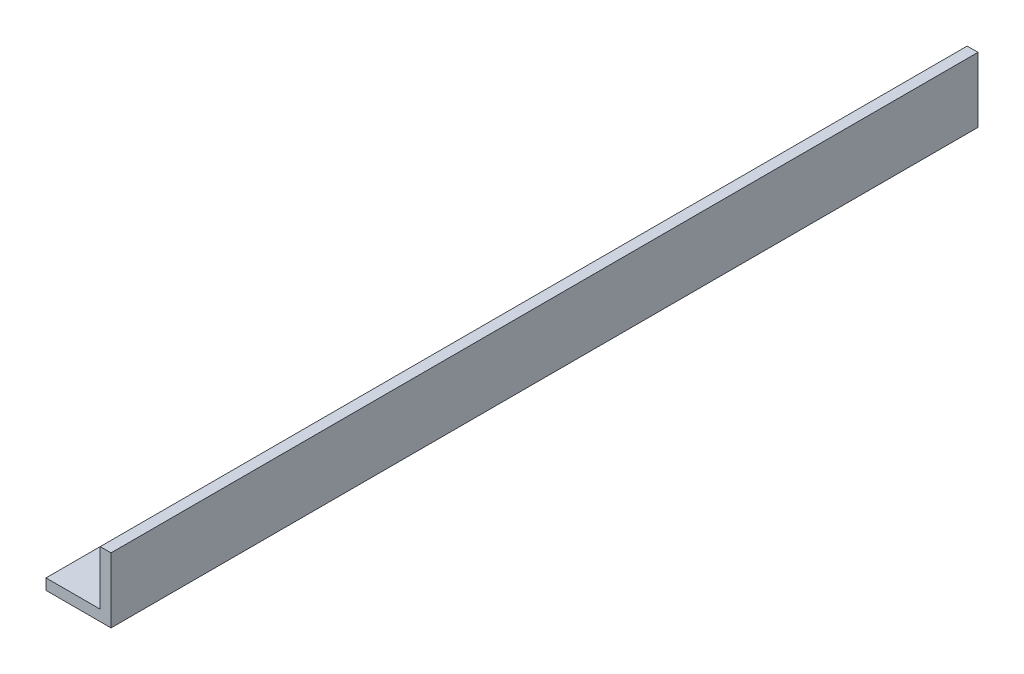
SolidWorks part; units mm, degrees
ref_plane "Front Plane" through (0, 0, 0) normal (0, 0, 1) x (1, 0, 0)
ref_plane "Top Plane" through (0, 0, 0) normal (0, 1, 0) x (1, 0, 0)
ref_plane "Right Plane" through (0, 0, 0) normal (1, 0, 0) x (0, 0, -1)
sketch "Sketch1" plane through (0, 0, 0) normal (0, 0, 1) x (1, 0, 0)
  line L0 (-4.7625, -4.7625) -> (4.7625, -4.7625) construction
  line L1 (4.7625, -4.7625) -> (4.7625, 4.7625) construction
  line L2 (4.7625, 4.7625) -> (3.175, 4.7625) construction
  line L3 (3.175, 4.7625) -> (3.175, -3.175) construction
  line L4 (3.175, -3.175) -> (-4.7625, -3.175) construction
  line L5 (-4.7625, -4.7625) -> (-4.7625, -3.175) construction
  line L6 (3.9688, 4.7625) -> (4.7625, 4.7625) construction
  line L7 (-4.7625, -3.9688) -> (-4.7625, -4.7625) construction
  line L8 (0, 0) -> (4.7625, 0) construction
  line L9 (0, 0) -> (0, -4.7625) construction
  point P3 (0, -4.7625)
  point P5 (3.175, -4.7625)
  point P8 (-4.7625, -4.7625)
  point P12 (-4.7625, -3.175)
  point P17 (3.175, 4.7625)
  dimension "Outside Height" = 9.525
  dimension "Outside Width" = 9.525
  dimension "Wall Thickness" = 1.5875
  dimension "Inside Width" = 7.9375
  dimension "Inside Height" = 7.9375
sketch "Sketch2" plane through (0, 0, 0) normal (1, 0, 0) x (0, 0, -1)
  line L0 (0, 0) -> (609.6, 0) construction
  line L1 (0, 0) -> (-609.6, 0) construction
  line L2 (0, -4.7625) -> (609.6, -4.7625) construction
  line L3 (609.6, -4.7625) -> (609.6, 0) construction
  line L4 (0, -4.7625) -> (-609.6, -4.7625) construction
  line L5 (-609.6, -4.7625) -> (-609.6, 0) construction
  point P3 (600.075, 0)
  point P5 (609.6, 0)
  point P6 (-600.075, 0)
  point P7 (-609.6, 0)
  dimension "D1" = 9.525
  dimension "D2" = 9.525
  dimension "Length" = 1219.2
sketch "Sketch3" plane through (0, 0, 0) normal (0, 0, 1) x (1, 0, 0)
  line L0 (3.175, -3.175) -> (-4.7625, -3.175) construction
  line L1 (-4.7625, -4.7625) -> (-4.7625, -3.175) construction
  line L2 (-4.7625, -4.7625) -> (4.7625, -4.7625) construction
  line L3 (4.7625, -4.7625) -> (4.7625, 4.7625) construction
  line L4 (4.7625, 4.7625) -> (3.175, 4.7625) construction
  line L5 (3.175, 4.7625) -> (3.175, -3.175) construction
  line L6 (3.175, -3.175) -> (-4.7625, -3.175)
  line L7 (-4.7625, -4.7625) -> (-4.7625, -3.175)
  line L8 (-4.7625, -4.7625) -> (4.7625, -4.7625)
  line L9 (4.7625, -4.7625) -> (4.7625, 4.7625)
  line L10 (4.7625, 4.7625) -> (3.175, 4.7625)
  line L11 (3.175, 4.7625) -> (3.175, -3.175)
extrude "Boss-Extrude1" add sketch "Sketch3" along normal mid plane 127
equation "\"D2@Sketch2\"=\"D1@Sketch2\""
equation "\"D1@Sketch2\"=\"outside height@sketch1\""
